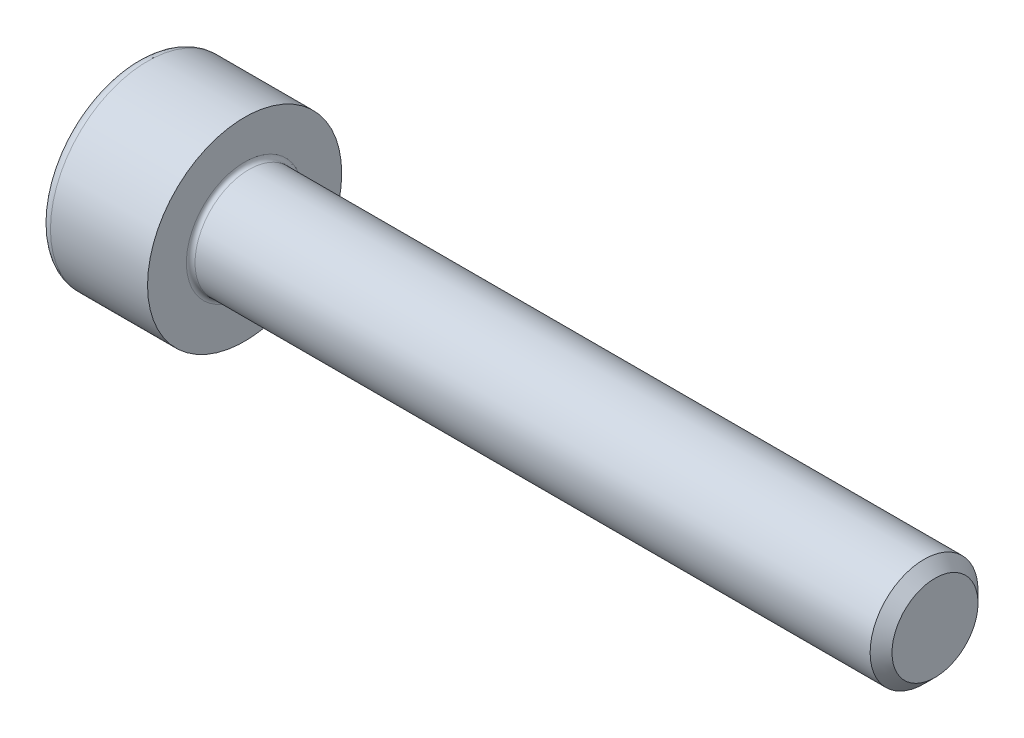
SolidWorks part; units mm, degrees
ref_plane "Plane1" through (0, 0, 0) normal (0, 0, 1) x (1, 0, 0)
ref_plane "Plane2" through (0, 0, 0) normal (0, 1, 0) x (1, 0, 0)
ref_plane "Plane3" through (0, 0, 0) normal (1, 0, 0) x (0, 0, -1)
sketch "BodySke" plane through (0, 0, 0) normal (0, 0, 1) x (1, 0, 0)
  line L0 (0, 0) -> (0, 2.25)
  line L1 (0, 2.25) -> (2.5, 2.25)
  line L2 (2.5, 2.25) -> (2.5, 1.25)
  line L3 (2.5, 1.25) -> (18.2465, 1.25)
  line L4 (18.5, 0.9965) -> (18.5, 0)
  line L5 (18.5, 0) -> (0, 0)
  line L6 (-31.75, 0) -> (127, 0) construction
  line L8 (18.5, 0.9965) -> (18.2465, 1.25)
  line L10 (18.5, -0.9965) -> (18.2465, -1.25) construction
  line L11 (2.95, 9.525) -> (2.95, 3.175) construction
  line L12 (10.5, 9.525) -> (10.5, 3.175) construction
  line L13 (-41.5, 9.525) -> (-41.5, 3.175) construction
  dimension "Diameter" = 2.5
  dimension "Head_ht" = 2.5
  dimension "Length" = 16
  dimension "Body_ch_ang" = 45
  dimension "Head_dia" = 4.5
  dimension "Minor_dia" = 1.993
  dimension "Advance" = 0.45
  dimension "Thread_nom" = 8
  dimension "Thread_length" = 60
revolve "Base-Revolve" add sketch "BodySke"
cosmetic thread "ThreadCosmetic" [suppressed]
fillet "Fillet1" radius 0.1 1 edges at (2.5, 0, 1.25)
fillet "Fillet2" radius 0.25 1 edges at (0, 0, 2.25)
sketch "Sketch2" plane through (0, 0, 0) normal (0, 0, 1) x (1, 0, 0)
  line L0 (0, 1.01) -> (1.1, 1.01)
  line L1 (1.1, 1.01) -> (1.6831, 0)
  line L2 (-31.75, 0) -> (127, 0) construction
  line L3 (1.6831, 0) -> (0, 0)
  line L4 (0, 0) -> (0, 1.01)
  line L6 (0, 0) -> (47.625, 0) construction
  dimension "D1" = 1.01
  dimension "D2" = 60
  dimension "Depth" = 1.1
revolve "Hex-PreBroach" cut sketch "Sketch2" angle 360 about L6
sketch "Sketch3" plane through (0, 0, 0) normal (-1, 0, 0) x (0, 0.5, 0.866)
  line L0 (0.5831, 1.01) -> (-0.5831, 1.01)
  line L1 (-0.5831, 1.01) -> (-1.1662, 0)
  line L2 (0.5831, 1.01) -> (1.1662, 0)
  line L3 (0.5831, -1.01) -> (1.1662, 0)
  line L4 (0.5831, -1.01) -> (-0.5831, -1.01)
  line L5 (-0.5831, -1.01) -> (-1.1662, 0)
  dimension "D1" = 1.01
  dimension "D2" = 1.01
  dimension "Hex_size" = 2.02
extrude "Hex" cut sketch "Sketch3" against normal blind 1.1
sketch "ThdSchSke" plane through (0, 0, 0) normal (0, 0, 1) x (1, 0, 0)
  line L0 (10.5, -0.9965) -> (10.3225, -1.25)
  line L1 (10.5, -0.9965) -> (10.6775, -1.25)
  line L2 (10.6775, -1.25) -> (10.6775, -1.5625)
  line L3 (-3.175, 0) -> (5.1513, 0) construction
  line L4 (0, 2) -> (0, -2) construction
  line L5 (10.6775, -1.5625) -> (10.3225, -1.5625)
  line L6 (10.3225, -1.5625) -> (10.3225, -1.25)
  dimension "Thread_minor" = 1.993
  dimension "Diameter" = 2.5
  dimension "Start" = 10.5
  dimension "SideAngle" = 55
  dimension "VeeAngle" = 70
  dimension "Overcut" = 3.125
revolve "ThreadSchematic" [suppressed] cut sketch "ThdSchSke" angle 360 about L3
pattern_linear "ThdSchPat" [suppressed]
equation "\"D2@Sketch3\" = \"Hex_size@Sketch3\" / 2"
equation "\"D1@Sketch3\" = \"Hex_size@Sketch3\" / 2"
equation "\"D1@Sketch2\" = \"Hex_size@Sketch3\" / 2"
equation "\"Thread_minor@ThreadCosmetic\"  =  \"Minor_dia@BodySke\""
equation "\"Depth@Sketch2\" =  \"Key_eng@Hex\""
equation "\"Thread_length@ThreadCosmetic\" = ((sgn( (\"Length@BodySke\" - \"Advance@BodySke\" * 3.0) - \"Thread_nom@BodySke\" )-1)*( (\"Length@BodySke\" - \"Advance@BodySke\" * 3.0) - \"Thread_nom@BodySke\" ))/-2+ \"Thread_nom@BodySke\""
equation "\"Thread_minor@ThdSchSke\" = \"Minor_dia@BodySke\""
equation "\"Diameter@ThdSchSke\" = \"Diameter@BodySke\""
equation "\"Overcut@ThdSchSke\" = \"Diameter@BodySke\" * 1.25"
equation "\"Start@ThdSchSke\" = \"Head_ht@BodySke\" + \"Length@BodySke\" - \"Thread_length@ThreadCosmetic\"  '---Non-countersunk---"
equation "\"Num_threads@ThdSchPat\" = int( \"Thread_length@ThreadCosmetic\" / \"Advance@BodySke\" + 0.999 )  + 1"
equation "\"Advance@ThdSchPat\" = \"Thread_length@ThreadCosmetic\" /  (\"Num_threads@ThdSchPat\" - 1) 'relax it"
equation "\"Num_threads@ThdSchPat\" = \"Num_threads@ThdSchPat\" - sgn( \"Num_threads@ThdSchPat\" - 1) '---chamfered tips only---"
